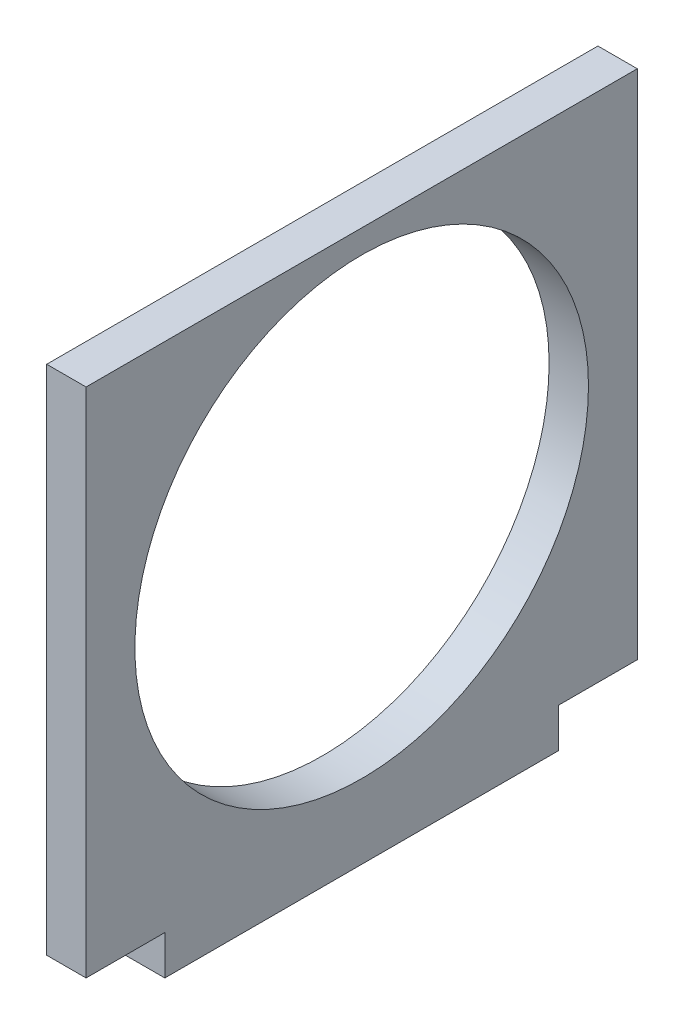
SolidWorks part; units mm, degrees
ref_plane "Front Plane" through (0, 0, 0) normal (0, 0, 1) x (1, 0, 0)
ref_plane "Top Plane" through (0, 0, 0) normal (0, 1, 0) x (1, 0, 0)
ref_plane "Right Plane" through (0, 0, 0) normal (1, 0, 0) x (0, 0, -1)
sketch "Sketch1" plane through (0, 0, 0) normal (1, 0, 0) x (0, 0, -1)
  line L1 (0, 0) -> (44.45, 0)
  line L2 (0, 0) -> (0, 44.45)
  line L3 (0, 44.45) -> (44.45, 44.45)
  line L4 (44.45, 0) -> (44.45, 44.45)
  dimension "D1" = 44.45
  dimension "D2" = 44.45
extrude "Boss-Extrude1" add sketch "Sketch1" along normal blind 3.175
sketch "Sketch2" plane through (3.175, 0, 0) normal (1, 0, 0) x (0, 0, -1)
  line L0 (6.985, 25.4) -> (37.465, 25.4) construction
  line L1 (22.225, 25.4) -> (22.225, 0) construction
  line L2 (0, 0) -> (44.45, 0) construction
  line L3 (6.985, 24.6062) -> (37.465, 24.6063) construction
  line L4 (0, 0) -> (6.35, 0)
  line L5 (0, 0) -> (0, 3.175)
  line L6 (0, 3.175) -> (6.35, 3.175)
  line L7 (6.35, 0) -> (6.35, 3.175)
  line L8 (44.45, 0) -> (38.1, 0)
  line L9 (44.45, 0) -> (44.45, 3.175)
  line L10 (44.45, 3.175) -> (38.1, 3.175)
  line L11 (38.1, 0) -> (38.1, 3.175)
  circle A0 centre (6.985, 25.4) radius 0.7938 construction
  circle A1 centre (37.465, 25.4) radius 0.7937 construction
  circle A2 centre (22.225, 17.2085) radius 5.9246 construction
  circle A3 centre (22.225, 24.2697) radius 18.288
  point P24 (0, 0)
  point P25 (22.225, 21.3996)
  dimension "D6" = 1.5875
  dimension "D7" = 3.175
  dimension "D8" = 11.8491
  dimension "D9" = 8.1915
  dimension "D10" = 36.576
  dimension "D1" = 6.35
  dimension "D2" = 31.75
  dimension "D3" = 6.35
  dimension "D4" = 25.4
  dimension "D5" = 30.48
  dimension "D11" = 7.0612
extrude "Cut-Extrude1" cut sketch "Sketch2" against normal blind 3.175
